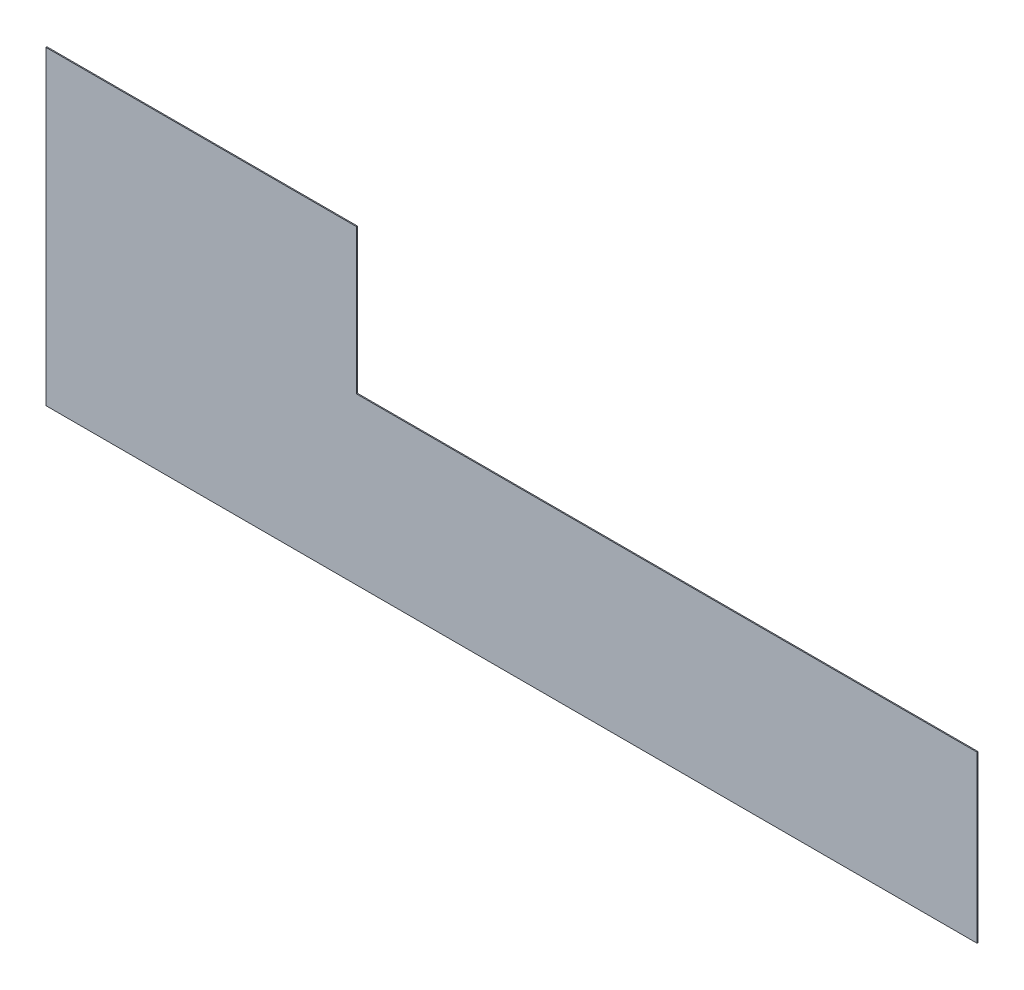
SolidWorks part; units mm, degrees
material "1023 Carbon Steel Sheet (SS)"
ref_plane "Front Plane" through (0, 0, 0) normal (0, 0, 1) x (1, 0, 0)
ref_plane "Top Plane" through (0, 0, 0) normal (0, 1, 0) x (1, 0, 0)
ref_plane "Right Plane" through (0, 0, 0) normal (1, 0, 0) x (0, 0, -1)
sketch "Sketch1" plane through (0, 0, 0) normal (0, 0, 1) x (1, 0, 0)
  line L0 (-444.5519, 140) -> (-444.5519, -160)
  line L1 (-144.5519, 0) -> (455.4481, 0)
  line L3 (-444.5519, -160) -> (455.4481, -160)
  line L4 (455.4481, 0) -> (455.4481, -160)
  line L9 (-444.5519, 140) -> (-144.5519, 140)
  line L10 (-144.5519, 0) -> (-144.5519, 140)
  point P0 (0, 0)
  dimension "D1" = 900
  dimension "D2" = 600
  dimension "D3" = 160
  dimension "D4" = 300
extrude "Boss-Extrude1" add sketch "Sketch1" along normal blind 1
